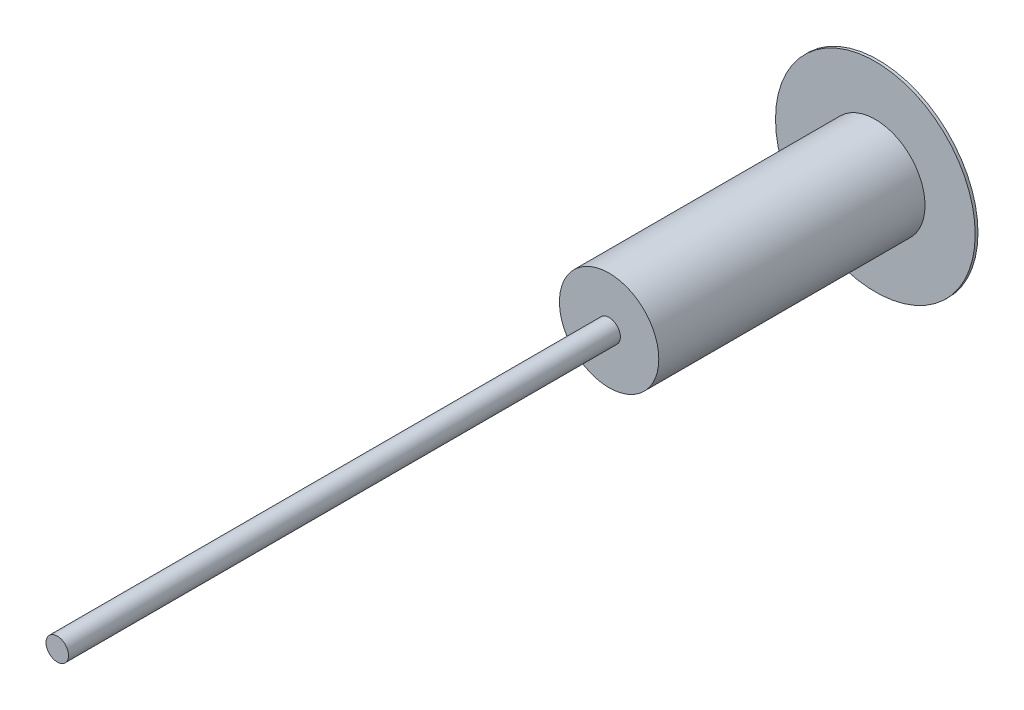
SolidWorks part; units mm, degrees
other "Markup1"
sketch "Sketch6" plane through (500, -500, -1363.6) normal (1, 0, 0) x (0, 0, -1)
ref_plane "Top Plane" through (0, 0, 0) normal (0, 0, 1) x (1, 0, 0)
ref_plane "Right Plane" through (0, 0, 0) normal (0, 1, 0) x (1, 0, 0)
ref_plane "Front Plane" through (0, 0, 0) normal (1, 0, 0) x (0, 0, -1)
sketch "Sketch1" plane through (0, 0, 0) normal (0, 0, 1) x (1, 0, 0)
  circle A0 centre (0, 0) radius 50.8
  dimension "D1" = 101.6
extrude "Boss-Extrude1" add sketch "Sketch1" against normal blind 2050 and the other way blind 1650
sketch "Sketch2" plane through (0, 0, -2050) normal (0, 0, 1) x (1, 0, 0)
  circle A0 centre (0, 0) radius 450
  dimension "D1" = 900
extrude "Boss-Extrude2" add sketch "Sketch2" along normal blind 12.7
sketch "Sketch3" plane through (0, 0, -2037.3) normal (0, 0, 1) x (1, 0, 0)
  circle A0 centre (0, 0) radius 223.901
  dimension "D1" = 447.802
extrude "Boss-Extrude3" add sketch "Sketch3" along normal blind 1200
